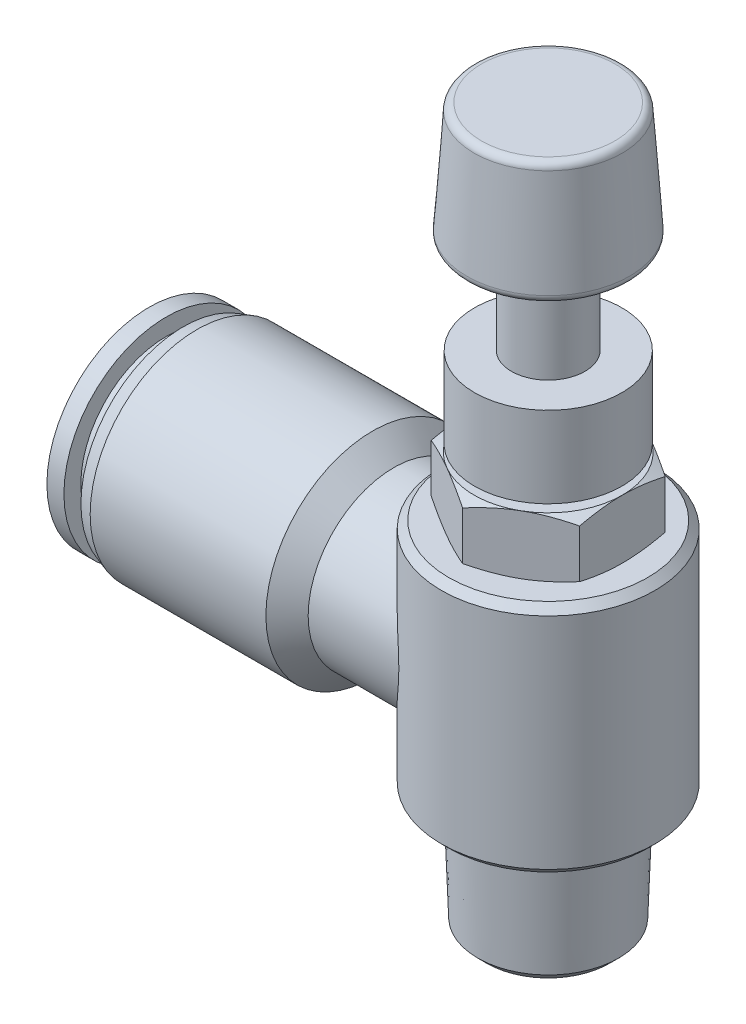
SolidWorks part; units mm, degrees
ref_plane "Front Plane" through (0, 0, 0) normal (0, 0, 1) x (1, 0, 0)
ref_plane "Top Plane" through (0, 0, 0) normal (0, 1, 0) x (1, 0, 0)
ref_plane "Right Plane" through (0, 0, 0) normal (1, 0, 0) x (0, 0, -1)
ref_plane "Plane1" through (0, 0, 0) normal (0, 0, 1) x (1, 0, 0)
sketch "Sketch1" plane through (0, 0, 0) normal (0, 0, 1) x (1, 0, 0)
  line L0 (0, 32.3) -> (4.4993, 32.3)
  line L1 (4.998, 31.8349) -> (5.4838, 24.8888)
  line L2 (4.985, 24.3539) -> (2.4768, 24.3539)
  line L3 (2.4768, 24.3539) -> (2.4768, 17.8321)
  line L4 (2.4768, 17.8321) -> (4.9655, 17.8321)
  line L5 (4.9655, 17.8321) -> (4.9655, 12.3692)
  line L6 (4.9655, 12.3692) -> (4, 12.3692)
  line L7 (4, 12.3692) -> (4, 11.8692)
  line L8 (4, 11.8692) -> (5, 11.8692)
  line L9 (5, 11.8692) -> (6, 11.4029)
  line L10 (6, 11.4029) -> (6, 8.3663)
  line L11 (6, 8.3663) -> (5, 7.9)
  line L12 (5, 7.9) -> (6.7, 7.9)
  line L13 (6.7, 7.9) -> (7.2, 7.4)
  line L14 (7.2, 7.4) -> (7.2, -7.4)
  line L15 (7.2, -7.4) -> (6.7, -7.9)
  line L16 (6.7, -7.9) -> (5.004, -7.9)
  line L17 (5.004, -7.9) -> (4.7458, -15.2952)
  line L18 (4.7458, -15.2952) -> (4.141, -15.9)
  line L19 (4.141, -15.9) -> (0, -15.9)
  line L20 (0, -15.9) -> (0, 32.3)
  line L21 (0, -15.9) -> (0, 32.3) construction
  arc A0 (4.4993, 32.3) -> (4.998, 31.8349) centre (4.4993, 31.8) cw
  arc A1 (5.4838, 24.8888) -> (4.985, 24.3539) centre (4.985, 24.8539) cw
revolve "Revolve1" add sketch "Sketch1" angle 360 about L21
ref_plane "Plane2" through (0, 11.8692, 0) normal (0, 1, 0) x (1, 0, 0)
sketch "Sketch2" plane through (0, 11.8692, 0) normal (0, 1, 0) x (1, 0, 0)
  line L0 (-6.5, -3.7528) -> (0, -7.5056)
  line L1 (0, -7.5056) -> (6.5, -3.7528)
  line L2 (6.5, -3.7528) -> (6.5, 3.7528)
  line L3 (6.5, 3.7528) -> (0, 7.5056)
  line L4 (0, 7.5056) -> (-6.5, 3.7528)
  line L5 (-6.5, 3.7528) -> (-6.5, -3.7528)
  line L6 (-5, -2.8868) -> (0, -5.7735)
  line L7 (0, -5.7735) -> (5, -2.8868)
  line L8 (5, -2.8868) -> (5, 2.8868)
  line L9 (5, 2.8868) -> (0, 5.7735)
  line L10 (0, 5.7735) -> (-5, 2.8868)
  line L11 (-5, 2.8868) -> (-5, -2.8868)
extrude "Cut-Extrude1" cut sketch "Sketch2" against normal blind 3.9692
ref_plane "Plane3" through (0, 0, 0) normal (0, 0, 1) x (1, 0, 0)
sketch "Sketch3" plane through (0, 0, 0) normal (0, 0, 1) x (1, 0, 0)
  line L0 (-26.9, 4) -> (0, 4)
  line L1 (0, 4) -> (0, 5.7744)
  line L2 (0, 5.7744) -> (-10.4104, 5.7744)
  line L3 (-10.4104, 5.7744) -> (-11.836, 7.2)
  line L4 (-11.836, 7.2) -> (-23.6831, 7.2)
  line L5 (-23.6831, 7.2) -> (-24.6064, 6.9)
  line L6 (-24.6064, 6.9) -> (-24.6064, 5.76)
  line L7 (-24.6064, 5.76) -> (-25.7532, 5.76)
  line L8 (-25.7532, 5.76) -> (-25.7532, 6.9)
  line L9 (-25.7532, 6.9) -> (-26.9, 6.9)
  line L10 (-26.9, 6.9) -> (-26.9, 4)
  line L11 (0, 0) -> (-26.9, 0) construction
revolve "Revolve2" add sketch "Sketch3" angle 360 about L11
